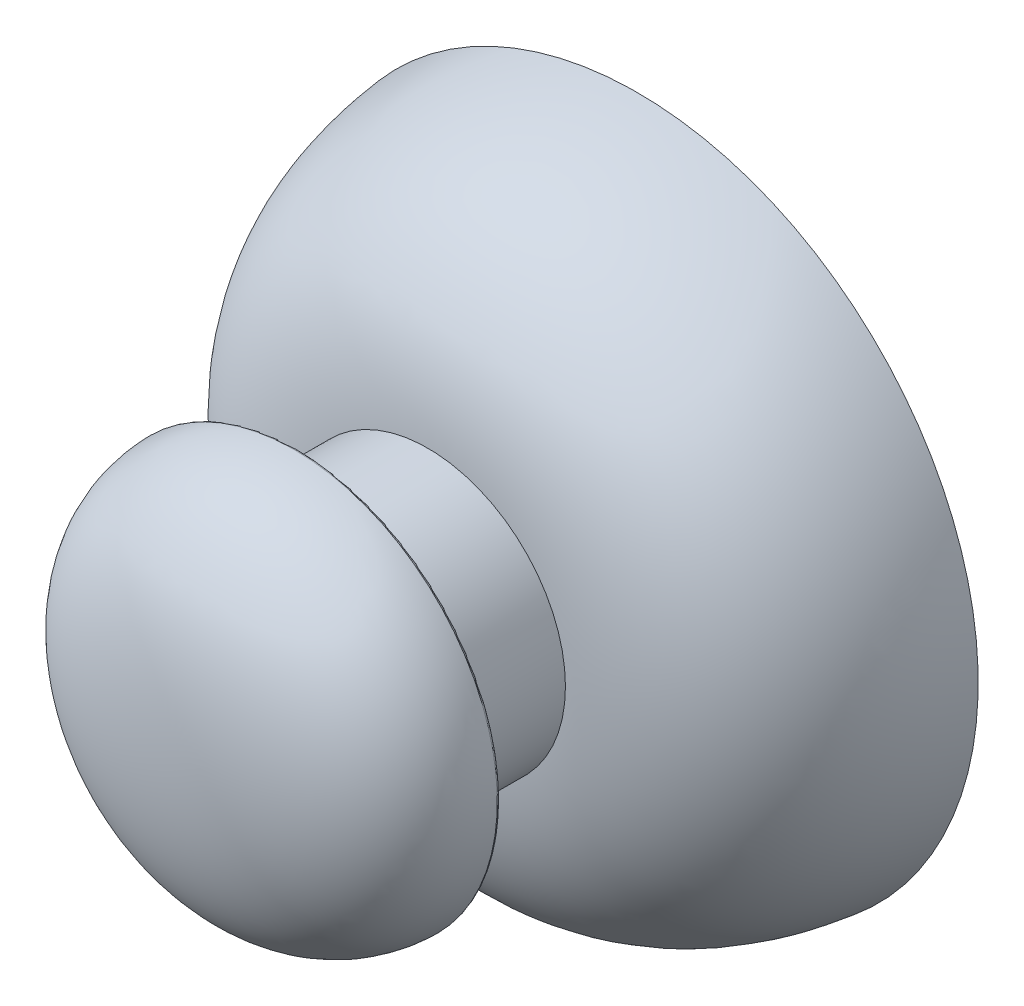
SolidWorks part; units mm, degrees
ref_plane "Front" through (0, 0, 0) normal (0, 0, 1) x (1, 0, 0)
ref_plane "Top" through (0, 0, 0) normal (0, 1, 0) x (1, 0, 0)
ref_plane "Right" through (0, 0, 0) normal (1, 0, 0) x (0, 0, -1)
sketch "草图1" plane through (0, 0, 0) normal (0, 0, 1) x (1, 0, 0)
  circle A0 centre (0, 0) radius 13
sketch "草图2" plane through (0, 0, 0) normal (0, 0, 1) x (1, 0, 0)
  circle A1 centre (0, 0) radius 5.25
extrude "凸台-拉伸1" add sketch "草图2" along normal blind 8
sketch "草图3" plane through (0, 0, 0) normal (1, 0, 0) x (0, 0, -1)
  line L0 (0, 0) -> (-11.876, 0) construction
  line L1 (-8, 0) -> (-8, -5.25)
  line L2 (-8, 0) -> (0, 0)
  line L3 (0, 13) -> (0, -13) construction
  line L4 (0, 0) -> (0, -13)
  spline S0 degree 3 poles (0, -13) (-5.0689, -12.4569) (-7.7467, -9.679) (-8, -5.25) knots 0 0 0 0 1 1 1 1
revolve "旋转1" add sketch "草图3" angle 360 about L0
sketch "草图4" plane through (0, 0, 8) normal (0, 0, 1) x (1, 0, 0)
  circle A0 centre (0, 0) radius 5.25
extrude "凸台-拉伸2" add sketch "草图4" along normal blind 5
sketch "草图5" plane through (0, 0, 13) normal (0, 0, 1) x (1, 0, 0)
  circle A0 centre (0, 0) radius 7.7547
sketch "草图6" plane through (0, 0, 0) normal (1, 0, 0) x (0, 0, -1)
  line L0 (-13, 0) -> (-18, 0)
  line L1 (-13, 7.7547) -> (-13, -7.7547) construction
  line L2 (-13, 7.7547) -> (-13, 0)
  line L3 (-13, 0) -> (-21.5976, 0) construction
  spline S0 degree 3 poles (-18, 0) (-18, 7.564) (-13.9393, 7.7547) (-13, 7.7547) knots 0 0 0 0 1 1 1 1
revolve "旋转2" add sketch "草图6" angle 360 about L3
fillet "圆角1" radius 0.1 2 edges at (-7.7547, 0, 13) (5.25, 0, 13)
